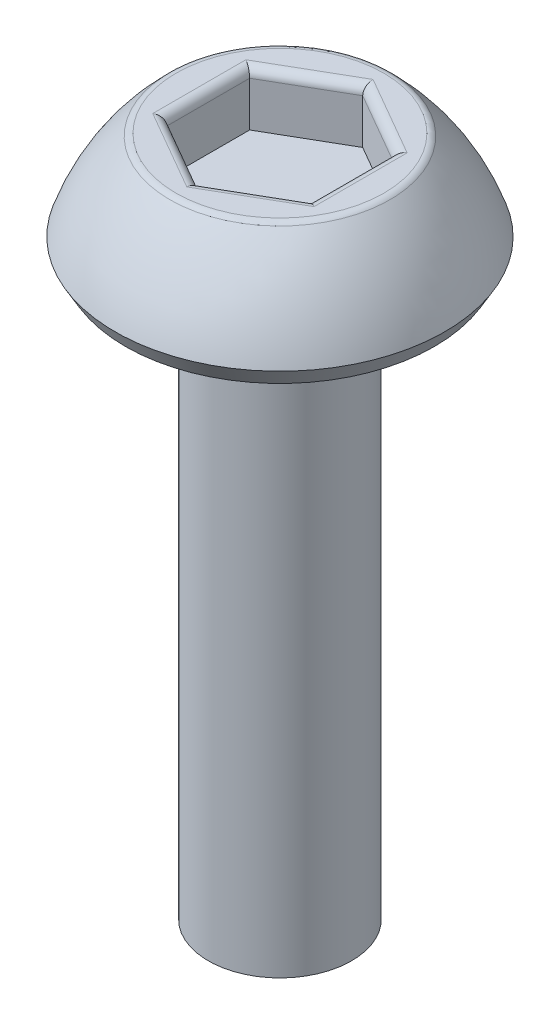
SolidWorks part; units mm, degrees
ref_plane "Front Plane" through (0, 0, 0) normal (0, 0, 1) x (1, 0, 0)
ref_plane "Top Plane" through (0, 0, 0) normal (0, 1, 0) x (1, 0, 0)
ref_plane "Right Plane" through (0, 0, 0) normal (1, 0, 0) x (0, 0, -1)
sketch "Sketch1" plane through (0, 0, 0) normal (1, 0, 0) x (0, 0, -1)
  line L0 (0, 0) -> (0, 1.5) construction
  line L1 (0, 1.5) -> (-1.5, 1.5)
  line L3 (-2.3, 0.25) -> (-2.1557, 0)
  line L4 (-2.1557, 0) -> (-1, 0)
  line L5 (-1, 0) -> (-1, -8)
  line L6 (-1, -8) -> (0, -8)
  line L7 (0, -8) -> (0, 1.5)
  line L8 (0, 0) -> (-1, 0) construction
  arc A0 (-1.5, 1.5) -> (-2.3, 0.25) centre (0.5483, -0.6919) ccw
  dimension "D5" = 3
  dimension "D1" = 1.5
  dimension "D2" = 2.3
  dimension "D3" = 1.5
  dimension "D4" = 0.25
  dimension "D6" = 60
  dimension "D7" = 1
  dimension "D8" = 8
  dimension "D9" = 2.3
revolve "Revolve1" add sketch "Sketch1" angle 360 about L7
sketch "Sketch2" plane through (0, 1.5, 0) normal (0, 1, 0) x (1, 0, 0)
  line L1 (0, 1.1547) -> (-1, 0.5774)
  line L2 (-1, 0.5774) -> (-1, -0.5774)
  line L3 (-1, -0.5774) -> (0, -1.1547)
  line L4 (0, -1.1547) -> (1, -0.5774)
  line L5 (1, -0.5774) -> (1, 0.5774)
  line L6 (1, 0.5774) -> (0, 1.1547)
  circle A0 centre (0, 0) radius 1 construction
  dimension "D1" = 2
extrude "Cut-Extrude1" cut sketch "Sketch2" against normal blind 0.75
fillet "Fillet1" radius 0.125 7 edges at (0, 1.5, -1.5) (-0.5, 1.5, 0.866) (0.5, 1.5, 0.866) (1, 1.5, 0) (0.5, 1.5, -0.866) (-0.5, 1.5, -0.866) (-1, 1.5, 0)
